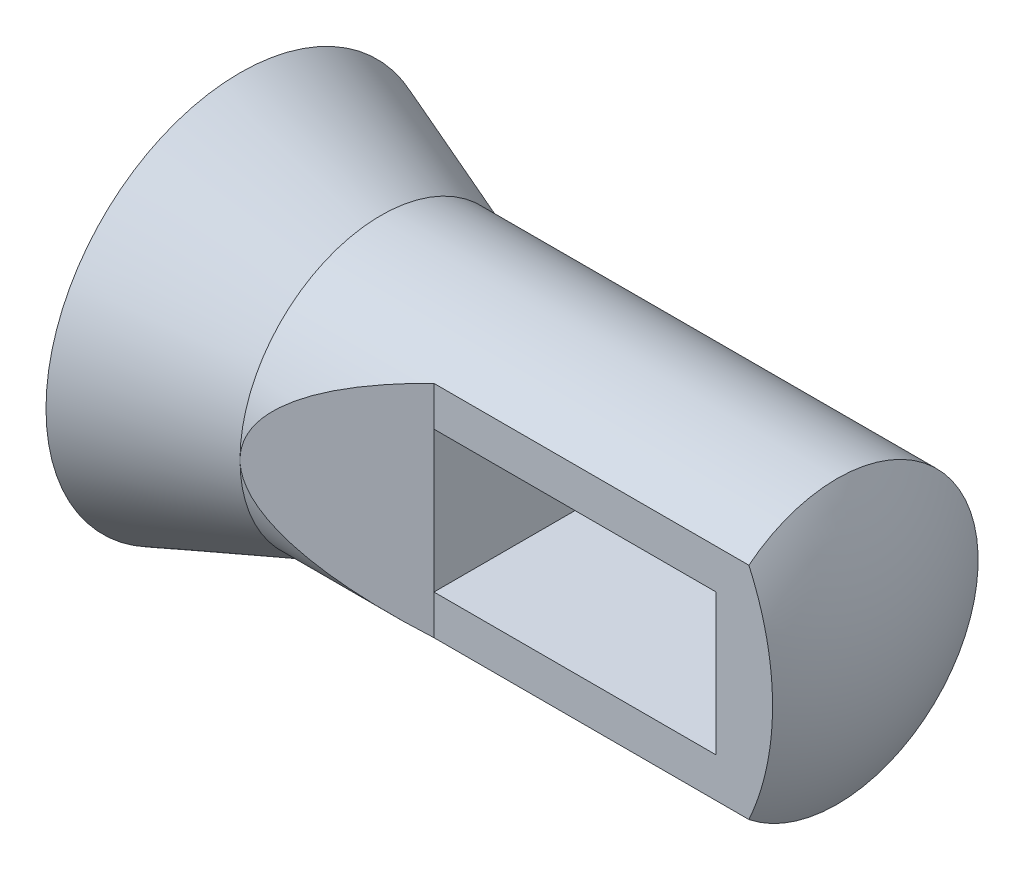
SolidWorks part; units mm, degrees
ref_plane "Front Plane" through (0, 0, 0) normal (0, 0, 1) x (1, 0, 0)
ref_plane "Top Plane" through (0, 0, 0) normal (0, 1, 0) x (1, 0, 0)
ref_plane "Right Plane" through (0, 0, 0) normal (1, 0, 0) x (0, 0, -1)
sketch "Sketch1" plane through (0, 0, 0) normal (0, 0, 1) x (1, 0, 0)
  line L0 (0, 0) -> (114.3, 0) construction
  line L1 (0, 0) -> (0, 34.925)
  line L2 (0, 34.925) -> (25.4, 25.4)
  line L3 (25.4, 25.4) -> (107.4941, 25.4)
  line L4 (114.3, 0) -> (114.3, 62.3199) construction
  line L5 (0, 0) -> (114.3, 0)
  arc A0 (107.4941, 25.4) -> (114.3, 0) centre (63.5, 0) cw
  dimension "D5" = 50.8
  dimension "D1" = 114.3
  dimension "D2" = 34.925
  dimension "D3" = 25.4
  dimension "D4" = 25.4
revolve "Revolve1" add sketch "Sketch1" angle 360 about L0
sketch "Sketch3" plane through (0, 0, 0) normal (0, 1, 0) x (1, 0, 0)
  line L0 (25.4, -25.4) -> (50.8, -15.875)
  line L1 (50.8, -15.875) -> (114.3, -15.875)
  line L2 (114.3, -15.875) -> (114.3, -25.4)
  line L3 (114.3, -25.4) -> (25.4, -25.4)
  line L4 (0, -34.925) -> (25.4, -25.4) construction
  line L6 (25.4, 0) -> (114.3, 0) construction
  line L7 (25.4, -25.4) -> (25.4, 25.4) construction
  arc A0 (107.4941, -25.4) -> (107.4941, 25.4) centre (63.5, 0) ccw construction
  dimension "D1" = 15.875
extrude "Cut-Extrude2" cut sketch "Sketch3" against normal through all and the other way through all
sketch "Sketch4" plane through (0, 0, 15.875) normal (0, 0, 1) x (1, 0, 0)
  line L0 (50.8, 0) -> (111.7558, 0) construction
  line L1 (50.8, -19.8279) -> (50.8, 19.8279) construction
  line L2 (50.8, -12.7) -> (101.6, -12.7)
  line L3 (101.6, -12.7) -> (101.6, 12.7)
  line L4 (50.8, 12.7) -> (101.6, 12.7)
  line L5 (50.8, 12.7) -> (50.8, -12.7)
  arc A0 (107.4941, -19.8279) -> (107.4941, 19.8279) centre (63.5, 0) ccw construction
  point P11 (101.6, 0)
  dimension "D1" = 12.7
  dimension "D2" = 50.8
extrude "Cut-Extrude3" cut sketch "Sketch4" against normal through all
